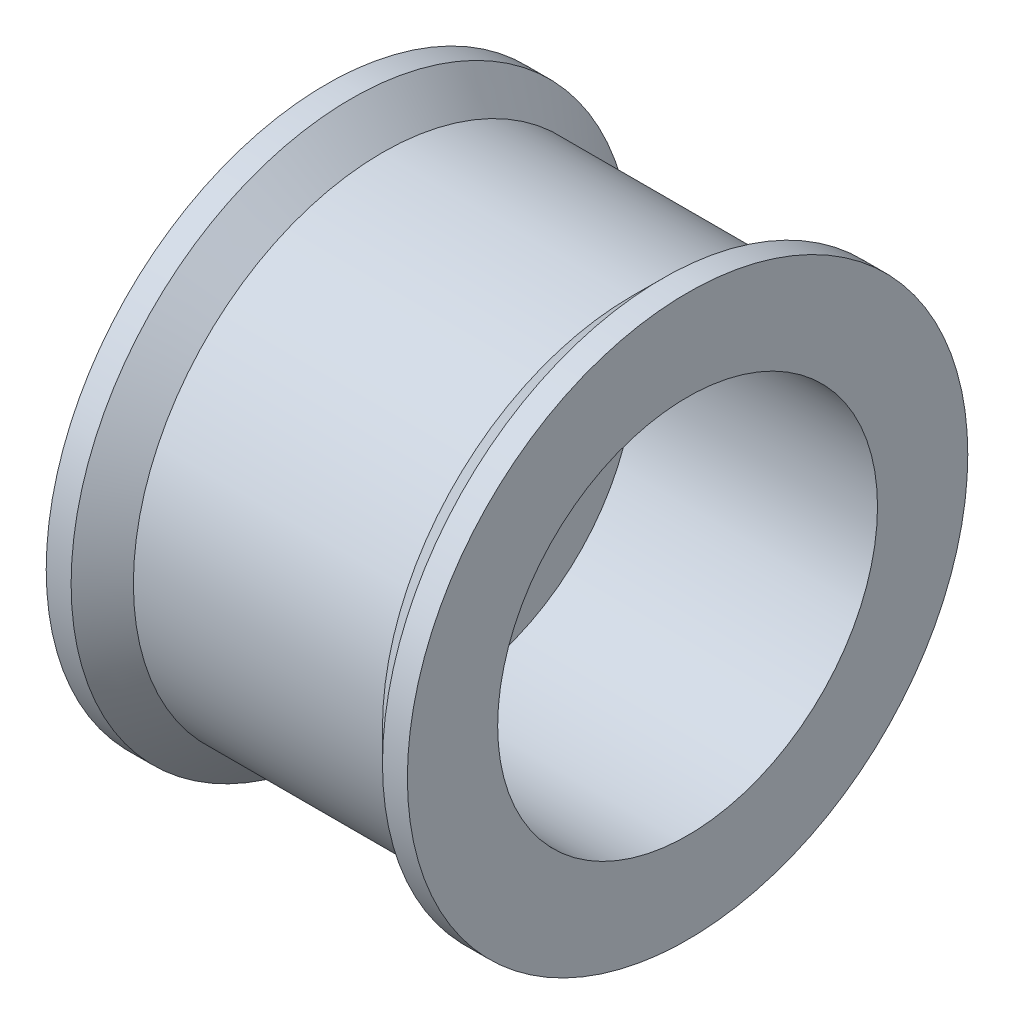
SolidWorks part; units mm, degrees
material "ABS"
ref_plane "Front Plane" through (0, 0, 0) normal (0, 0, 1) x (1, 0, 0)
ref_plane "Top Plane" through (0, 0, 0) normal (0, 1, 0) x (1, 0, 0)
ref_plane "Right Plane" through (0, 0, 0) normal (1, 0, 0) x (0, 0, -1)
sketch "Sketch1" plane through (0, 0, 0) normal (0, 0, 1) x (1, 0, 0)
  line L0 (0, 0) -> (8.902, 0) construction
  line L1 (-2.9, 1.5) -> (-2.9, 4.5)
  line L2 (-2.5, 4.5) -> (-2, 4)
  line L3 (-2, 4) -> (2, 4)
  line L4 (2, 4) -> (2.5, 4.5)
  line L5 (2.9, 4.5) -> (2.9, 1.5)
  line L6 (2.9, 1.5) -> (-2.9, 1.5)
  line L7 (0, 1.5) -> (0, 0) construction
  line L8 (-2.9, 4.5) -> (-2.5, 4.5)
  line L9 (2.5, 4.5) -> (2.9, 4.5)
  line L10 (0, 4) -> (0, 1.5) construction
  dimension "D1" = 4
  dimension "D2" = 1.5
  dimension "D3" = 45
  dimension "D4" = 5.8
  dimension "D5" = 4
  dimension "D6" = 4.5
revolve "Revolve1" add sketch "Sketch1" angle 360 about L0
sketch "Sketch3" plane through (0, 0, 0) normal (1, 0, 0) x (0, 0, -1)
  circle A0 centre (0, 0) radius 3.05
  dimension "D1" = 6.1
extrude "Cut-Extrude1" cut sketch "Sketch3" along normal blind 10 and the other way blind 1
